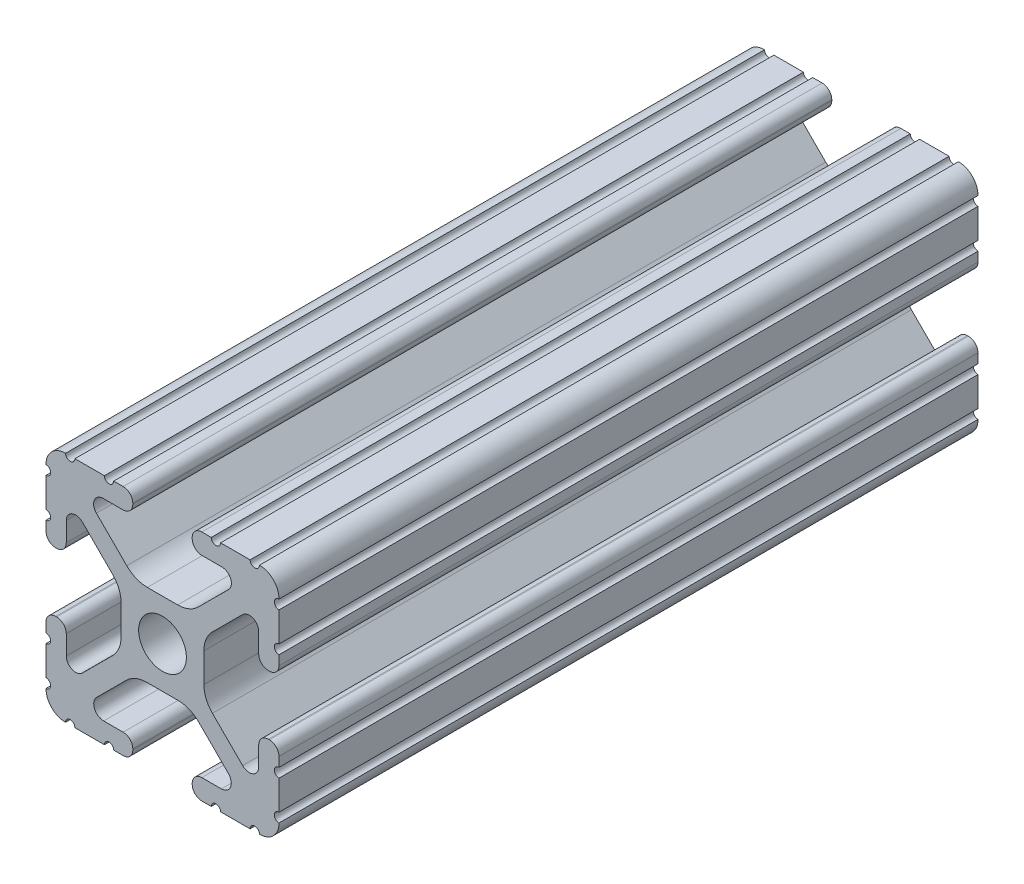
SolidWorks part; units mm, degrees
ref_plane "Front Plane" through (0, 0, 0) normal (0, 0, 1) x (1, 0, 0)
ref_plane "Top Plane" through (0, 0, 0) normal (0, 1, 0) x (1, 0, 0)
ref_plane "Right Plane" through (0, 0, 0) normal (1, 0, 0) x (0, 0, -1)
sketch "Sketch1" plane through (0, 0, 0) normal (0, 0, 1) x (1, 0, 0)
  line L0 (-7.207, 8.7244) -> (-3.8983, 5.4232)
  line L1 (-4.2875, 10.4902) -> (-6.4768, 10.4902)
  line L2 (-3.2385, 11.651) -> (-3.2385, 11.5392)
  line L3 (-5.3171, 12.7) -> (-4.2875, 12.7)
  line L4 (0, 13.4005) -> (0, -14.8534) construction
  line L5 (12.7, 0) -> (-13.9989, 0) construction
  line L6 (-9.5504, 12.7) -> (-6.3331, 12.7)
  line L7 (-12.7, 6.3331) -> (-12.7, 9.5504)
  line L8 (-12.7, 4.2875) -> (-12.7, 5.3171)
  line L9 (-11.5392, 3.2385) -> (-11.651, 3.2385)
  line L10 (-10.4902, 6.4021) -> (-10.4902, 4.2875)
  line L11 (-5.441, 3.8408) -> (-8.7371, 7.1294)
  line L12 (-4.5085, -1.5932) -> (-4.5085, 1.5932)
  line L13 (-1.7093, -4.4958) -> (1.7093, -4.4958)
  line L14 (3.9523, -5.4237) -> (7.1797, -8.6452)
  line L15 (6.4164, -10.4902) -> (4.2875, -10.4902)
  line L16 (3.2385, -11.5392) -> (3.2385, -11.651)
  line L17 (4.2875, -12.7) -> (5.3171, -12.7)
  line L18 (6.3331, -12.7) -> (9.5504, -12.7)
  line L19 (12.7, -9.5504) -> (12.7, -6.3331)
  line L20 (12.7, -5.3171) -> (12.7, -4.2875)
  line L21 (11.651, -3.2385) -> (11.5392, -3.2385)
  line L22 (10.4902, -4.2875) -> (10.4902, -6.4021)
  line L23 (8.7371, -7.1294) -> (5.441, -3.8408)
  line L24 (4.5085, -1.5932) -> (4.5085, 1.5932)
  line L25 (5.441, 3.8408) -> (8.7371, 7.1294)
  line L26 (10.4902, 6.4021) -> (10.4902, 4.2875)
  line L27 (11.5392, 3.2385) -> (11.651, 3.2385)
  line L28 (12.7, 4.2875) -> (12.7, 5.3171)
  line L29 (12.7, 6.3331) -> (12.7, 9.5504)
  line L30 (9.5504, 12.7) -> (6.3331, 12.7)
  line L31 (5.3171, 12.7) -> (4.2875, 12.7)
  line L32 (3.2385, 11.651) -> (3.2385, 11.5392)
  line L33 (4.2875, 10.4902) -> (6.4768, 10.4902)
  line L34 (7.207, 8.7244) -> (3.8983, 5.4232)
  line L35 (1.6558, 4.4958) -> (-1.6558, 4.4958)
  line L36 (-8.7371, -7.1294) -> (-5.441, -3.8408)
  line L37 (-10.4902, -4.2875) -> (-10.4902, -6.4021)
  line L38 (-11.651, -3.2385) -> (-11.5392, -3.2385)
  line L39 (-12.7, -5.3171) -> (-12.7, -4.2875)
  line L40 (-12.7, -9.5504) -> (-12.7, -6.3331)
  line L41 (-6.3331, -12.7) -> (-9.5504, -12.7)
  line L42 (-4.2875, -12.7) -> (-5.3171, -12.7)
  line L43 (-3.2385, -11.5392) -> (-3.2385, -11.651)
  line L44 (-6.4164, -10.4902) -> (-4.2875, -10.4902)
  line L45 (-3.9523, -5.4237) -> (-7.1797, -8.6452)
  arc A0 (-7.207, 8.7244) -> (-6.4768, 10.4902) centre (-6.4768, 9.4563) cw
  arc A1 (-3.2385, 11.5392) -> (-4.2875, 10.4902) centre (-4.2875, 11.5392) cw
  arc A2 (-4.2875, 12.7) -> (-3.2385, 11.651) centre (-4.2875, 11.651) cw
  arc A3 (-5.3171, 12.7) -> (-6.3331, 12.7) centre (-5.8251, 12.7) cw
  arc A4 (-9.5504, 12.7) -> (-10.5664, 12.6998) centre (-10.0584, 12.7) cw
  arc A5 (-12.6998, 10.5664) -> (-10.5664, 12.6998) centre (-10.5918, 10.5918) cw
  arc A6 (-12.6998, 10.5664) -> (-12.7, 9.5504) centre (-12.7, 10.0584) cw
  arc A7 (-12.7, 6.3331) -> (-12.7, 5.3171) centre (-12.7, 5.8251) cw
  arc A8 (-11.651, 3.2385) -> (-12.7, 4.2875) centre (-11.651, 4.2875) cw
  arc A9 (-10.4902, 4.2875) -> (-11.5392, 3.2385) centre (-11.5392, 4.2875) cw
  circle A10 centre (0, 0) radius 2.6035
  arc A11 (-10.4902, 6.4021) -> (-8.7371, 7.1294) centre (-9.4628, 6.4021) cw
  arc A12 (-5.441, 3.8408) -> (-4.5085, 1.5932) centre (-7.6835, 1.5932) cw
  arc A13 (-4.5085, -1.5932) -> (-5.441, -3.8408) centre (-7.6835, -1.5932) cw
  arc A14 (-8.7371, -7.1294) -> (-10.4902, -6.4021) centre (-9.4628, -6.4021) cw
  arc A15 (-1.7093, -4.4958) -> (-3.9523, -5.4237) centre (-1.7093, -7.6708) ccw
  arc A16 (3.9523, -5.4237) -> (1.7093, -4.4958) centre (1.7093, -7.6708) ccw
  arc A17 (6.4164, -10.4902) -> (7.1797, -8.6452) centre (6.4164, -9.4098) ccw
  arc A18 (4.2875, -10.4902) -> (3.2385, -11.5392) centre (4.2875, -11.5392) ccw
  arc A19 (3.2385, -11.651) -> (4.2875, -12.7) centre (4.2875, -11.651) ccw
  arc A20 (6.3331, -12.7) -> (5.3171, -12.7) centre (5.8251, -12.7) ccw
  arc A21 (10.5664, -12.6998) -> (9.5504, -12.7) centre (10.0584, -12.7) ccw
  arc A22 (10.5664, -12.6998) -> (12.6998, -10.5664) centre (10.5918, -10.5918) ccw
  arc A23 (12.7, -9.5504) -> (12.6998, -10.5664) centre (12.7, -10.0584) ccw
  arc A24 (12.7, -5.3171) -> (12.7, -6.3331) centre (12.7, -5.8251) ccw
  arc A25 (12.7, -4.2875) -> (11.651, -3.2385) centre (11.651, -4.2875) ccw
  arc A26 (11.5392, -3.2385) -> (10.4902, -4.2875) centre (11.5392, -4.2875) ccw
  arc A27 (8.7371, -7.1294) -> (10.4902, -6.4021) centre (9.4628, -6.4021) ccw
  arc A28 (4.5085, -1.5932) -> (5.441, -3.8408) centre (7.6835, -1.5932) ccw
  arc A29 (5.441, 3.8408) -> (4.5085, 1.5932) centre (7.6835, 1.5932) ccw
  arc A30 (10.4902, 6.4021) -> (8.7371, 7.1294) centre (9.4628, 6.4021) ccw
  arc A31 (10.4902, 4.2875) -> (11.5392, 3.2385) centre (11.5392, 4.2875) ccw
  arc A32 (11.651, 3.2385) -> (12.7, 4.2875) centre (11.651, 4.2875) ccw
  arc A33 (12.7, 6.3331) -> (12.7, 5.3171) centre (12.7, 5.8251) ccw
  arc A34 (12.6998, 10.5664) -> (12.7, 9.5504) centre (12.7, 10.0584) ccw
  arc A35 (12.6998, 10.5664) -> (10.5664, 12.6998) centre (10.5918, 10.5918) ccw
  arc A36 (9.5504, 12.7) -> (10.5664, 12.6998) centre (10.0584, 12.7) ccw
  arc A37 (5.3171, 12.7) -> (6.3331, 12.7) centre (5.8251, 12.7) ccw
  arc A38 (4.2875, 12.7) -> (3.2385, 11.651) centre (4.2875, 11.651) ccw
  arc A39 (3.2385, 11.5392) -> (4.2875, 10.4902) centre (4.2875, 11.5392) ccw
  arc A40 (7.207, 8.7244) -> (6.4768, 10.4902) centre (6.4768, 9.4563) ccw
  arc A41 (1.6558, 4.4958) -> (3.8983, 5.4232) centre (1.6558, 7.6708) ccw
  arc A42 (-1.6558, 4.4958) -> (-3.8983, 5.4232) centre (-1.6558, 7.6708) cw
  arc A43 (-11.5392, -3.2385) -> (-10.4902, -4.2875) centre (-11.5392, -4.2875) cw
  arc A44 (-12.7, -4.2875) -> (-11.651, -3.2385) centre (-11.651, -4.2875) cw
  arc A45 (-12.7, -5.3171) -> (-12.7, -6.3331) centre (-12.7, -5.8251) cw
  arc A46 (-12.7, -9.5504) -> (-12.6998, -10.5664) centre (-12.7, -10.0584) cw
  arc A47 (-10.5664, -12.6998) -> (-12.6998, -10.5664) centre (-10.5918, -10.5918) cw
  arc A48 (-10.5664, -12.6998) -> (-9.5504, -12.7) centre (-10.0584, -12.7) cw
  arc A49 (-6.3331, -12.7) -> (-5.3171, -12.7) centre (-5.8251, -12.7) cw
  arc A50 (-3.2385, -11.651) -> (-4.2875, -12.7) centre (-4.2875, -11.651) cw
  arc A51 (-4.2875, -10.4902) -> (-3.2385, -11.5392) centre (-4.2875, -11.5392) cw
  arc A52 (-6.4164, -10.4902) -> (-7.1797, -8.6452) centre (-6.4164, -9.4098) cw
  dimension "D1" = 5.207
  dimension "D9" = 14.859
  dimension "D2" = 25.4
  dimension "D3" = 12.7
  dimension "D4" = 6.477
  dimension "D5" = 8.2042
  dimension "D6" = 9.017
  dimension "D8" = 2.2098
  dimension "D10" = 2.2098
extrude "Extrude1" add sketch "Sketch1" against normal blind 76.2
